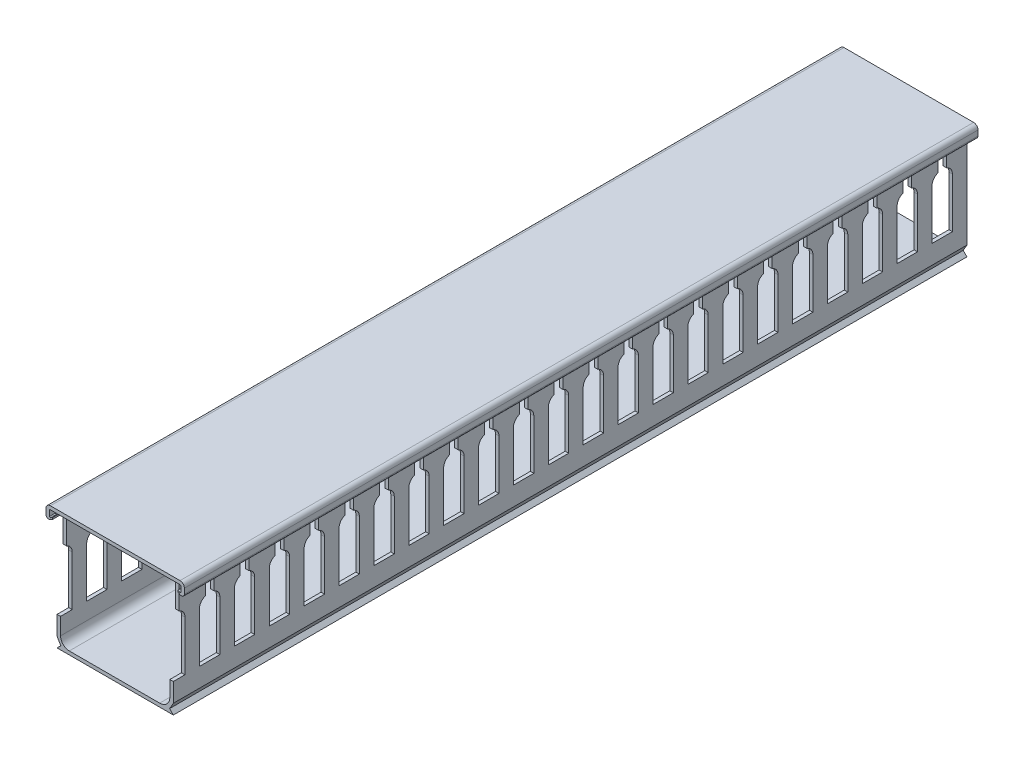
SolidWorks part; units mm, degrees
ref_plane "Front Plane" through (0, 0, 0) normal (0, 0, 1) x (1, 0, 0)
ref_plane "Top Plane" through (0, 0, 0) normal (0, 1, 0) x (1, 0, 0)
ref_plane "Right Plane" through (0, 0, 0) normal (1, 0, 0) x (0, 0, -1)
sketch "Sketch1" plane through (0, 0, 0) normal (0, 0, 1) x (1, 0, 0)
  line L0 (-20, 0) -> (20, 0)
  line L1 (-20, 3.5) -> (-20, 38.546)
  line L2 (-20, 0) -> (-18.7189, 1.2811)
  line L3 (-18.7189, 1.2811) -> (-20, 3.5)
  line L4 (-22.4196, 37.589) -> (-20.381, 38.766)
  line L5 (0, 0) -> (0, -17.0643) construction
  line L6 (22.4196, 37.589) -> (22.5, 37.889)
  line L7 (22.4196, 37.589) -> (20.381, 38.766)
  line L8 (20, 3.5) -> (20, 38.546)
  line L9 (18.7189, 1.2811) -> (20, 3.5)
  line L10 (-22.4196, 37.589) -> (-22.5, 37.889)
  line L11 (20, 0) -> (18.7189, 1.2811)
  line L12 (-18.8, 4.2) -> (-18.8, 38.546)
  line L13 (18.8, 3.5) -> (18.8, 38.546) construction
  line L14 (-17.2865, 1.2) -> (20, 1.2) construction
  line L15 (-15.8, 1.2) -> (15.3, 1.2)
  line L16 (18.8, 4.7) -> (18.8, 38.546)
  line L17 (-17.2865, 1.2) -> (-18.8, 3.8215) construction
  line L18 (-17.2865, 1.2) -> (-17.2865, 1.2) construction
  line L19 (-18.8, 3.8215) -> (-18.8, 38.546) construction
  arc A0 (-22.5, 37.889) -> (-21.2623, 39.5936) centre (-17.1014, 35.2708) cw
  arc A1 (22.5, 37.889) -> (21.2623, 39.5936) centre (17.1014, 35.2708) ccw
  arc A2 (20.381, 38.766) -> (20, 38.546) centre (20.254, 38.546) ccw
  arc A3 (-21.2623, 39.5936) -> (-18.8, 38.546) centre (-20.254, 38.546) cw
  arc A4 (21.2623, 39.5936) -> (18.8, 38.546) centre (20.254, 38.546) ccw
  arc A5 (-15.8, 1.2) -> (-18.8, 4.2) centre (-15.8, 4.2) cw
  arc A6 (-20.381, 38.766) -> (-20, 38.546) centre (-20.254, 38.546) cw
  arc A7 (15.3, 1.2) -> (18.8, 4.7) centre (15.3, 4.7) ccw
  arc A8 (-20.981, 39.8052) -> (-18.8, 38.546) centre (-20.254, 38.546) cw construction
  arc A9 (20.981, 39.8052) -> (18.8, 38.546) centre (20.254, 38.546) ccw construction
  dimension "D1" = 0.3
  dimension "D2" = 6
  dimension "D3" = 60
  dimension "D5" = 0.254
  dimension "D6" = 1.2
  dimension "D11" = 3
  dimension "D13" = 3.5
  dimension "D14" = 40
  dimension "D7" = 45
  dimension "D8" = 30
  dimension "D4" = 75
  dimension "D9" = 3.5
  dimension "D10" = 2.5
  dimension "D12" = 40
extrude "Boss-Extrude2" add sketch "Sketch1" along normal mid plane 1000 contours L0 L11 L9 L8 A2 L7 L6 A1 A4 L16 A7 L15 A5 L12 A3 A0 L10 L4 A6 L1 L3 L2
sketch "Sketch2" plane through (0, 0, 0) normal (1, 0, 0) x (0, 0, -1)
  line L0 (490, 30) -> (490, 40)
  line L1 (-500, 0) -> (500, 0) construction
  line L2 (500, 3.5) -> (500, 38.546) construction
  line L3 (488, 10) -> (495, 10)
  line L4 (495, 10) -> (495, 27.1716)
  line L6 (490, 40) -> (493, 40)
  line L7 (493, 30) -> (493, 40)
  line L8 (488, 10) -> (488, 27.1716)
  line L10 (500, 40) -> (-500, 40) construction
  arc A0 (495, 27.1716) -> (493, 30) centre (492, 27.1716) ccw
  arc A1 (488, 27.1716) -> (490, 30) centre (491, 27.1716) cw
  point P22 (491.5, 10)
  point P23 (491.5, 40)
  dimension "D1" = 3
  dimension "D2" = 10
  dimension "D3" = 10
  dimension "D4" = 7
  dimension "D5" = 5
  dimension "D6" = 3
extrude "Cut-Extrude1" cut sketch "Sketch2" against normal blind 82.296 and the other way blind 151.13
pattern_linear "LPattern1" count 83 spacing 12 along (0, 0, 1) of "Cut-Extrude1"
sketch "Sketch3" plane through (0, 0, -500) normal (0, 0, 1) x (1, 0, 0)
  line L0 (-22.6, 37.9) -> (-22.6, 39.7) construction
  line L1 (-22.6, 37.8781) -> (-22.6, 39.7)
  line L2 (22.3, 40) -> (-22.3, 40)
  line L4 (22.6, 37.8781) -> (22.6, 39.7)
  line L5 (22.6, 37.9) -> (22.6, 39.7) construction
  line L6 (22.3, 41.2) -> (-22.3, 41.2)
  line L7 (-22.3, 37.034) -> (-21.6, 37.4381)
  line L8 (-21.6, 37.4381) -> (-21.6, 38.0155)
  line L9 (-23.8, 37.9) -> (-23.8, 39.7)
  line L10 (-21.6, 38.0155) -> (-22.219, 37.6581)
  line L12 (22.3, 37.034) -> (21.6, 37.4381)
  line L14 (21.6, 38.0155) -> (22.219, 37.6581)
  line L15 (23.8, 37.9) -> (23.8, 39.7)
  line L16 (21.6, 37.4381) -> (21.6, 38.0155)
  arc A0 (-23.8, 37.9) -> (-22.3, 37.034) centre (-22.8, 37.9) ccw
  arc A1 (-22.6, 37.8781) -> (-22.219, 37.6581) centre (-22.346, 37.8781) ccw
  arc A2 (22.3, 37.034) -> (23.8, 37.9) centre (22.8, 37.9) ccw
  arc A3 (-22.3, 41.2) -> (-23.8, 39.7) centre (-22.3, 39.7) ccw
  arc A4 (-22.3, 40) -> (-22.6, 39.7) centre (-22.3, 39.7) ccw
  arc A5 (22.3, 41.2) -> (23.8, 39.7) centre (22.3, 39.7) cw
  arc A6 (22.3, 40) -> (22.6, 39.7) centre (22.3, 39.7) cw
  arc A7 (22.6, 37.8781) -> (22.219, 37.6581) centre (22.346, 37.8781) cw
  arc A9 (-18.8, 38.546) -> (-21.2623, 39.5936) centre (-20.254, 38.546) ccw construction
  point P35 (0, 40)
  dimension "D2" = 2.2
  dimension "D3" = 0.254
  dimension "D4" = 2.2
  dimension "D5" = 1.5
  dimension "D7" = 4.3
  dimension "D12" = 1
  dimension "D6" = 60
  dimension "D8" = 60
  dimension "D9" = 0.5
  dimension "D11" = 0.1
  dimension "D10" = 1.2
extrude "Boss-Extrude3" add sketch "Sketch3" along normal up to vertex separate body
sketch "Sketch4" plane through (0, 0, 500) normal (0, 0, 1) x (1, 0, 0)
  line L1 (-26.8347, 43.9626) -> (24.7337, 43.9626)
  line L2 (-26.8347, 43.9626) -> (-26.8347, -3.4039)
  line L3 (-26.8347, -3.4039) -> (24.7337, -3.4039)
  line L4 (24.7337, 43.9626) -> (24.7337, -3.4039)
extrude "Cut-Extrude2" cut sketch "Sketch4" against normal blind 727
